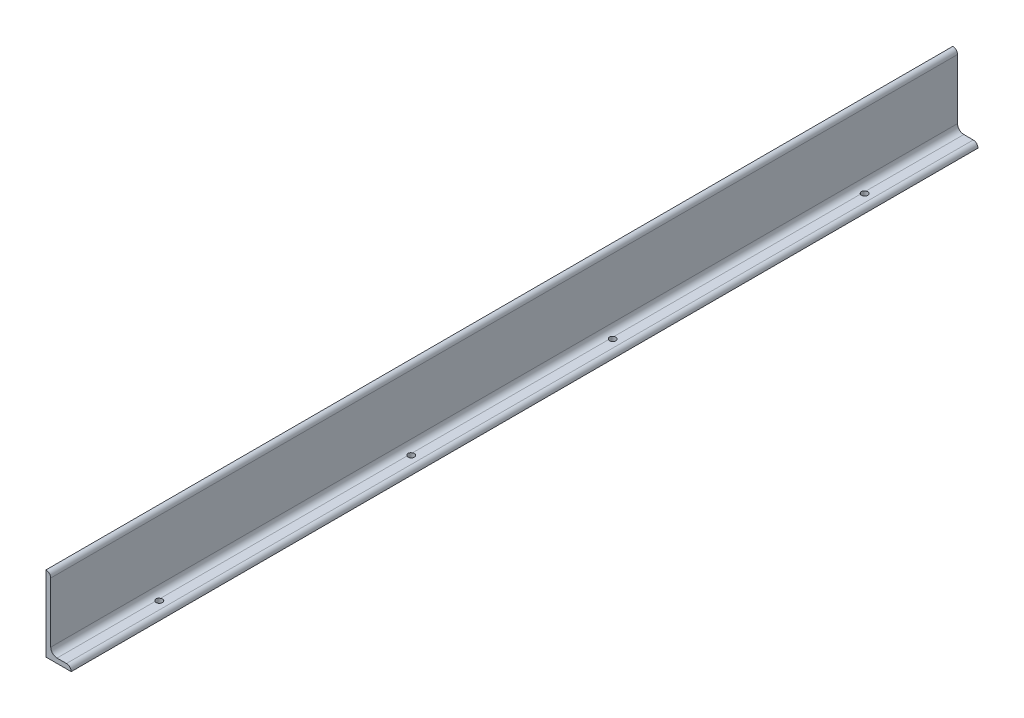
SolidWorks part; units mm, degrees
ref_plane "Front Plane" through (0, 0, 0) normal (0, 0, 1) x (1, 0, 0)
ref_plane "Top Plane" through (0, 0, 0) normal (0, 1, 0) x (1, 0, 0)
ref_plane "Right Plane" through (0, 0, 0) normal (1, 0, 0) x (0, 0, -1)
sketch "Sketch1" plane through (0, 0, 0) normal (0, 0, 1) x (1, 0, 0)
  line L0 (0, 0) -> (0, 152.4)
  line L1 (0, 152.4) -> (0.0051, 152.4)
  line L2 (9.525, 142.8801) -> (9.525, 22.225)
  line L3 (22.225, 9.525) -> (41.2801, 9.525)
  line L4 (50.8, 0.0051) -> (50.8, 0)
  line L5 (50.8, 0) -> (0, 0)
  arc A0 (50.8, 0.0051) -> (41.2801, 9.525) centre (41.2801, 0.0051) ccw
  arc A1 (0.0051, 152.4) -> (9.525, 142.8801) centre (0.0051, 142.8801) cw
  arc A2 (22.225, 9.525) -> (9.525, 22.225) centre (22.225, 22.225) cw
  circle A3 centre (0, 0) radius 12.7 construction
  dimension "D2" = 0.0051
  dimension "Radius_1" = 12.7
  dimension "Radius_2" = 12.7
  dimension "D1" = 9.525
  dimension "V_leg" = 152.4
  dimension "H_leg" = 50.8
  dimension "Thickness" = 9.525
  dimension "Flat_wid" = 0.0051
extrude "Boss-Extrude1" add sketch "Sketch1" along normal mid plane 1828.8
sketch "Sketch2" plane through (0, 0, 0) normal (0, -1, 0) x (1, 0, 0)
  line L0 (25.4, -914.4) -> (25.4, 914.4) construction
  line L1 (0, -914.4) -> (50.8, -914.4) construction
  line L2 (0, 914.4) -> (50.8, 914.4) construction
  circle A0 centre (25.4, -711.2) radius 6.35
  circle A1 centre (25.4, -203.2) radius 6.35
  circle A2 centre (25.4, 203.2) radius 6.35
  circle A3 centre (25.4, 711.2) radius 6.35
  dimension "D1" = 203.2
  dimension "D2" = 508
  dimension "D3" = 406.4
  dimension "D4" = 508
extrude "Cut-Extrude1" cut sketch "Sketch2" against normal through all
equation "\"D3@Sketch3\" = \"D2@Sketch3\""
